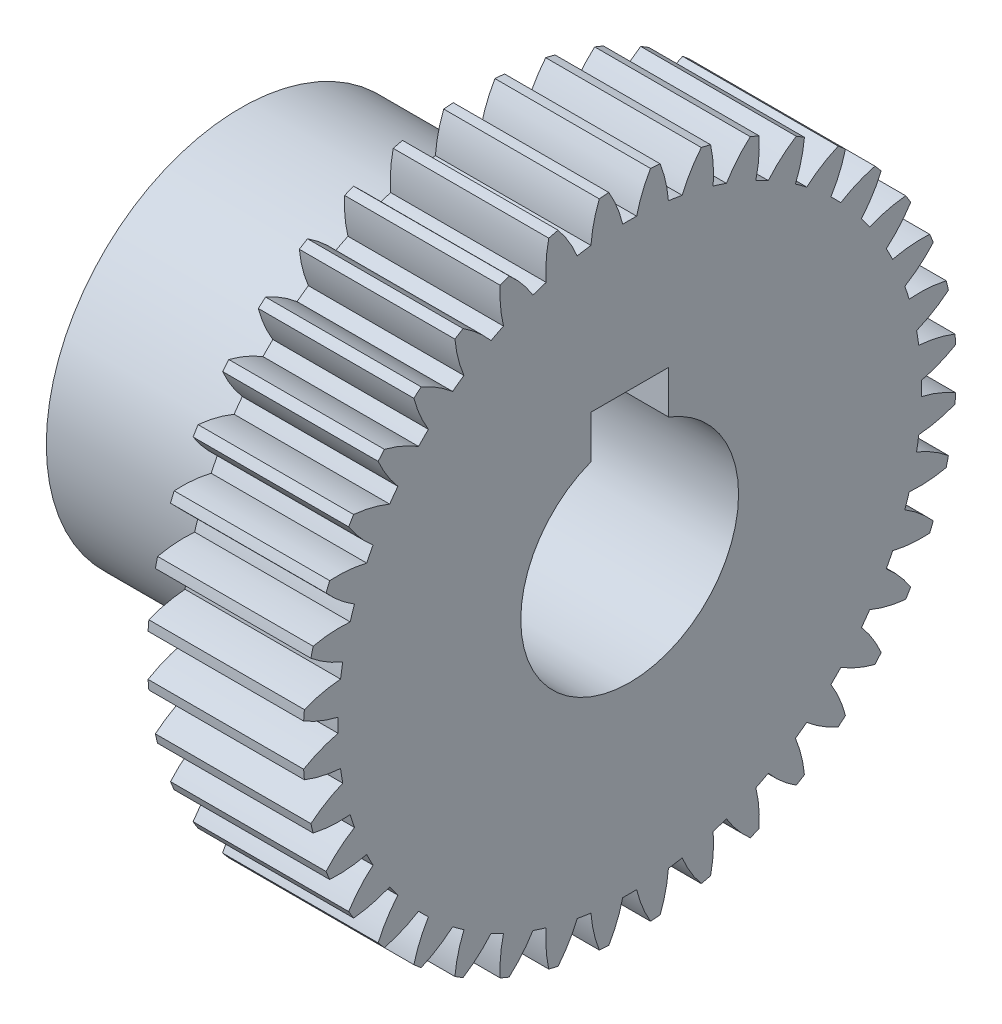
SolidWorks part; units mm, degrees
ref_plane "Plane1" through (0, 0, 0) normal (0, 0, 1) x (1, 0, 0)
ref_plane "Plane2" through (0, 0, 0) normal (0, 1, 0) x (1, 0, 0)
ref_plane "Plane3" through (0, 0, 0) normal (1, 0, 0) x (0, 0, -1)
sketch "HoldingSke" plane through (0, 0, 0) normal (0, 1, 0) x (1, 0, 0)
  line L0 (0, 0) -> (0.766, -0.6428)
  line L1 (-15, 0) -> (100, 0) construction
  line L2 (0, 0) -> (-2.1039, 2.3779)
  line L3 (0, 0) -> (-11.863, 4.5341)
  line L4 (0, 0) -> (6.6156, 5.5511)
  line L5 (0, 0) -> (-23.4238, -8.7364)
  line L6 (0, 0) -> (-7.4607, -5.0337)
  line L7 (-2.1039, 2.3779) -> (3.2774, 26.7919)
  line L8 (-76.2, 54.61) -> (-73.9, 54.61)
  line L9 (-71.009, 38.7566) -> (-53.1078, 45.2721)
  line L10 (-76.2, 71.12) -> (104.1128, 71.12)
  line L11 (0, 0) -> (-9, 0)
  line L12 (-76.2, 101.6) -> (-76.162, 101.6)
  line L13 (24.9733, 27.94) -> (52.9518, 28.4284)
  line L14 (24.9733, 27.94) -> (24.9743, 27.94)
  line L15 (24.9733, 27.94) -> (100.4006, 29.5858)
  line L16 (-63.627, -1) -> (-12.827, -1)
  circle A0 centre (0, 0) radius 7
  circle A1 centre (0, 0) radius 12.5
  circle A2 centre (0, 0) radius 12.5
  circle A3 centre (0, 0) radius 7
  dimension "MHD" = 25
  dimension "Hub_dia" = 25
  dimension "Bore" = 14
  dimension "MBD" = 14
  dimension "Num_teeth" = 40
  dimension "Pitch" = 1
  dimension "Overall_len" = 25
  dimension "Show_teeth" = 40
  dimension "Thickness" = 9
  dimension "OAL" = 25.0001
  dimension "T_dim" = 2.3
  dimension "Ap" = 20
  dimension "H" = 19.05
  dimension "Pitch_radius" = 180.3128
  dimension "Width" = 9
  dimension "Backlash" = 0.038
  dimension "Addendum_fac" = 1
  dimension "Dedendum_fac" = 1.25
  dimension "Clearance_fac" = 0.25
  dimension "Dedendum_add" = 0.001
  dimension "Module" = 1
sketch "BasProSke" plane through (0, 0, 0) normal (0, 1, 0) x (1, 0, 0)
  line L0 (-10, 0) -> (60, 0) construction
  line L1 (0, 0) -> (0, 21)
  line L2 (0, 0) -> (10, 0)
  line L3 (10, 0) -> (10, 21)
  line L4 (10, 21) -> (0, 21)
  dimension "Thickness" = 10
  dimension "Diameter" = 42
revolve "Base-Revolve" add sketch "BasProSke" angle 360 about L0
sketch "TooCutSke" plane through (0, 0, 0) normal (1, 0, 0) x (0, 0, -1)
  line L1 (0, 0) -> (0, 107) construction
  line L2 (0, 0) -> (-0.8517, 19.9819) construction
  line L3 (0, 0) -> (-3.1363, 39.8509) construction
  line L4 (-0.8517, 19.9819) -> (-1.5682, 19.9255) construction
  arc A0 (0.4487, 18.7436) -> (-0.4487, 18.7436) centre (0, 0) ccw
  arc A1 (1.3547, 20.9817) -> (-1.3547, 20.9817) centre (0, 0) ccw
  circle A2 centre (0, 0) radius 20 construction
  circle A3 centre (0, 0) radius 18.7939 construction
  arc A4 (-0.4487, 18.7436) -> (-1.3547, 20.9817) centre (-8.2322, 16.895) ccw
  arc A5 (1.3547, 20.9817) -> (0.4487, 18.7436) centre (8.2322, 16.895) ccw
  dimension "Root_dia" = 37.498
  dimension "Overcut_dia" = 42.0508
  dimension "Pitch_dia" = 40
  dimension "Base_dia" = 37.5877
  dimension "Flank_rad" = 8
  dimension "Half_ang" = 4.5
  dimension "Half_CT" = 0.7187
extrude "ToothCut" cut sketch "TooCutSke" along normal through all
fillet "Breaks" [suppressed] radius 0.02
fillet "RootFillets" [suppressed] radius 0.251
pattern_circular "TeethCuts" count 40 every 9 about axis through (-10, 0, 0) along (1, 0, 0) of "ToothCut", "RootFillets", "Breaks"
sketch "HubNeaOneSke" plane through (0, 0, 0) normal (-1, 0, 0) x (0, 0, 1)
  circle A0 centre (0, 0) radius 12.5
  dimension "Diameter" = 25
extrude "HubNearOne" add sketch "HubNeaOneSke" along normal blind 15.0001
sketch "HubNeaBotSke" plane through (0, 0, 0) normal (-1, 0, 0) x (0, 0, 1)
  circle A0 centre (0, 0) radius 12.5
  dimension "Diameter" = 25
extrude "HubNearBoth" [suppressed] add sketch "HubNeaBotSke" along normal blind 7.5
ref_plane "FarPln" through (10, 0, 0) normal (1, 0, 0) x (0, 0, -1)
sketch "HubFarSke" plane through (10, 0, 0) normal (1, 0, 0) x (0, 0, -1)
  circle A0 centre (0, 0) radius 12.5
  dimension "Diameter" = 25
extrude "HubFar" [suppressed] add sketch "HubFarSke" along normal blind 7.5
sketch "BorSke" plane through (0, 0, 0) normal (1, 0, 0) x (0, 0, -1)
  circle A0 centre (0, 0) radius 7
  dimension "Diameter" = 14
extrude "Bore" cut sketch "BorSke" along normal mid plane 50.0001
sketch "KeySke" plane through (0, 0, 0) normal (1, 0, 0) x (0, 0, -1)
  line L0 (-2.5, 0) -> (-2.5, 9.3)
  line L1 (-2.5, 9.3) -> (2.5, 9.3)
  line L2 (2.5, 9.3) -> (2.5, 0)
  line L3 (0, 0) -> (0, 34) construction
  line L4 (-2.5, 0) -> (2.5, 0)
  dimension "Offset" = 9.3
  dimension "Width" = 5
extrude "Keyway" cut sketch "KeySke" along normal mid plane 50.0001
pattern_circular "Keyway2" [suppressed] count 2 every 90 about axis through (-10, 0, 0) along (1, 0, 0)
equation "' \"Module@HoldingSke\" = 6.35"
equation "' \"Num_teeth@HoldingSke\" = 12"
equation "' \"Ap@HoldingSke\" =  20"
equation "' \"Ap@HoldingSke\" = 20"
equation "' \"Width@HoldingSke\" = 0.5 * 25.4"
equation "' \"Hub_dia@HoldingSke\"= 1 * 25.4"
equation "' \"Hub_dia@HoldingSke\" = 1 * 25.4"
equation "' \"Overall_len@HoldingSke\" = 1.0 * 25.4"
equation "' \"Bore@HoldingSke\" = 0.75 * 25.4"
equation "' \"T_dim@HoldingSke\" = 0.1 * 25.4"
equation "' \"Width@KeySke\" = 0.25 * 25.4"
equation "' \"Show_teeth@HoldingSke\" = 13"
equation "' \"Backlash@HoldingSke\" = 0.009 * 25.4"
equation "' \"Addendum_fac@HoldingSke\" = 1.0"
equation "' \"Dedendum_fac@HoldingSke\" = 1.25"
equation "' \"Dedendum_add@HoldingSke\" = 0.00005 * 25.4"
equation "' \"Clearance_fac@HoldingSke\" = 0.25"
equation "\"Pitch@HoldingSke\" = 1 / \"Module@HoldingSke\""
equation "\"Overcut_dia@TooCutSke\" = (\"Num_teeth@HoldingSke\" + 2 * \"Addendum_fac@HoldingSke\") / \"Pitch@HoldingSke\" + 0.002 * 25.4"
equation "\"Pitch_dia@TooCutSke\" = \"Num_teeth@HoldingSke\" / \"Pitch@HoldingSke\""
equation "\"Base_dia@TooCutSke\" = \"Num_teeth@HoldingSke\" / \"Pitch@HoldingSke\" * cos((\"Ap@HoldingSke\"  * 3.14159265 / 180))"
equation "\"Root_dia@TooCutSke\" = (\"Num_teeth@HoldingSke\" + 2) / \"Pitch@HoldingSke\" - 2 * (\"Addendum_fac@HoldingSke\" + \"Dedendum_fac@HoldingSke\") / \"Pitch@HoldingSke\" - \"Dedendum_add@HoldingSke\" * 2"
equation "\"Half_ang@TooCutSke\" = 180 / \"Num_teeth@HoldingSke\""
equation "\"Half_CT@TooCutSke\" = \"Num_teeth@HoldingSke\" / \"Pitch@HoldingSke\" * sin((3.14159265 / 2 / \"Num_teeth@HoldingSke\")) / 2 - 7 * \"Backlash@HoldingSke\" / 4"
equation "\"Flank_rad@TooCutSke\" = \"Num_teeth@HoldingSke\" / \"Pitch@HoldingSke\" / 5"
equation "\"Radius@RootFillets\" = \"Clearance_fac@HoldingSke\" / \"Pitch@HoldingSke\" + \"Dedendum_add@HoldingSke\""
equation "\"Break_rad@Breaks\" = 0.02 / \"Pitch@HoldingSke\""
equation "\"Thickness@HoldingSke\" = \"Width@HoldingSke\""
equation "\"OAL@HoldingSke\" = \"Thickness@HoldingSke\""
equation "\"MHD@HoldingSke\" = (\"Num_teeth@HoldingSke\" + 2) / \"Pitch@HoldingSke\" - 2 * (\"Addendum_fac@HoldingSke\" + \"Dedendum_fac@HoldingSke\")  / \"Pitch@HoldingSke\" - \"Dedendum_add@HoldingSke\" * 2"
equation "\"MBD@HoldingSke\" = (\"Num_teeth@HoldingSke\" + 2) / \"Pitch@HoldingSke\" - 2 * (\"Addendum_fac@HoldingSke\" + \"Dedendum_fac@HoldingSke\")  / \"Pitch@HoldingSke\" - \"Dedendum_add@HoldingSke\" * 2 - 0.002 * 25.4"
equation "\"MHD@HoldingSke\" = ((sgn( \"MHD@HoldingSke\" - \"Hub_dia@HoldingSke\" )-1)*( \"MHD@HoldingSke\" - \"Hub_dia@HoldingSke\" ))/-2+ \"Hub_dia@HoldingSke\""
equation "\"MBD@HoldingSke\" = ((sgn( \"MBD@HoldingSke\" - \"Bore@HoldingSke\" )-1)*( \"MBD@HoldingSke\" - \"Bore@HoldingSke\" ))/-2+ \"Bore@HoldingSke\""
equation "\"OAL@HoldingSke\" = ((sgn( \"OAL@HoldingSke\" - \"Overall_len@HoldingSke\" )+1)*( \"OAL@HoldingSke\" - \"Overall_len@HoldingSke\" ))/2 + \"Overall_len@HoldingSke\" + 0.000002 * 25.4"
equation "\"Num_teeth@TeethCuts\" = int( \"Show_teeth@HoldingSke\" ) + 1"
equation "\"Num_teeth@TeethCuts\" = ((sgn( \"Num_teeth@TeethCuts\" - \"Num_teeth@HoldingSke\" )-1)*( \"Num_teeth@TeethCuts\" - \"Num_teeth@HoldingSke\" ))/-2+ \"Num_teeth@HoldingSke\""
equation "\"Num_teeth@TeethCuts\" = ((sgn( \"Num_teeth@TeethCuts\" - 2.0)+1)*( \"Num_teeth@TeethCuts\" - 2.0))/2 +2.0"
equation "\"Angle@TeethCuts\" = 360.0 / \"Num_teeth@HoldingSke\""
equation "\"Diameter@BasProSke\" = (\"Num_teeth@HoldingSke\" + 2 * \"Addendum_fac@HoldingSke\") / \"Pitch@HoldingSke\""
equation "\"Thickness@BasProSke\"=10"
equation "' \"Fillet_rad@BasProSke\" =  \"Thickness@HoldingSke\" * 0.05"
equation "' \"Fillet_rad@BasProSke\" = \"Thickness@HoldingSke\" * 0.05"
equation "\"MHD@HoldingSke\" = ((sgn( \"MHD@HoldingSke\" - \"Root_dia@TooCutSke\" )-1)*( \"MHD@HoldingSke\" - \"Root_dia@TooCutSke\" ))/-2+ \"Root_dia@TooCutSke\""
equation "\"Diameter@HubNeaOneSke\" = \"MHD@HoldingSke\""
equation "\"Length@HubNearOne\" = \"OAL@HoldingSke\" - \"Thickness@BasProSke\""
equation "\"Diameter@HubNeaBotSke\" = \"MHD@HoldingSke\""
equation "\"Length@HubNearBoth\" = ( \"OAL@HoldingSke\" - \"Thickness@BasProSke\" ) / 2.0"
equation "\"Thickness@FarPln\" = \"Thickness@BasProSke\""
equation "\"Diameter@HubFarSke\" = \"MHD@HoldingSke\""
equation "\"Length@HubFar\" = ( \"OAL@HoldingSke\" - \"Thickness@BasProSke\" ) / 2.0"
equation "\"Diameter@BorSke\" = \"MBD@HoldingSke\""
equation "\"D1@Bore\" = \"OAL@HoldingSke\" * 2.0"
equation "\"D1@Keyway\" = \"OAL@HoldingSke\" * 2.0"
equation "\"Offset@KeySke\" = \"T_dim@HoldingSke\" + \"MBD@HoldingSke\" / 2.0"
